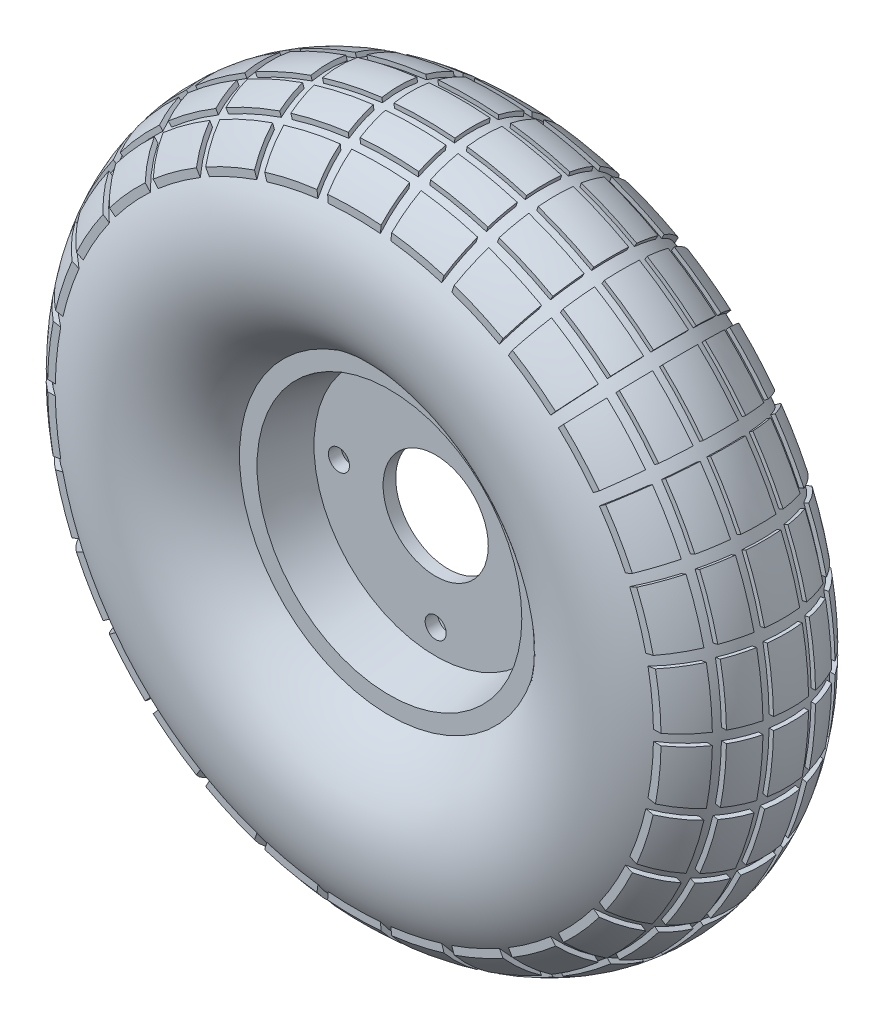
SolidWorks part; units mm, degrees
ref_plane "Front Plane" through (0, 0, 0) normal (0, 0, 1) x (1, 0, 0)
ref_plane "Top Plane" through (0, 0, 0) normal (0, 1, 0) x (1, 0, 0)
ref_plane "Right Plane" through (0, 0, 0) normal (1, 0, 0) x (0, 0, -1)
sketch "Sketch1" plane through (0, 0, 0) normal (1, 0, 0) x (0, 0, -1)
  line L0 (-19.05, 47.9669) -> (-19.05, 54.3169)
  line L1 (-19.05, 47.9669) -> (-2.286, 44.0981)
  line L2 (-2.286, 44.0981) -> (-2.286, 0)
  line L3 (-2.286, 0) -> (0, 0)
  line L4 (0, 0) -> (0, 52.3875)
  line L5 (0, 122.2375) -> (0, 125.4125)
  arc A0 (0, 125.4125) -> (-19.05, 54.3169) centre (0, 87.3125) ccw
  arc A1 (0, 122.2375) -> (0, 52.3875) centre (0, 87.3125) ccw
  dimension "D1" = 3.175
  dimension "D6" = 76.2
  dimension "D2" = 102.995
  dimension "D3" = 6.35
  dimension "D4" = 2.286
  dimension "D5" = 125.4125
  dimension "D7" = 19.05
  dimension "D8" = 52.3875
revolve "Revolve1" add sketch "Sketch1" angle 360 about L3
sketch "Sketch3" plane through (0, 0, 0) normal (1, 0, 0) x (0, 0, -1)
  line L0 (0, 125.4125) -> (0, 127)
  line L1 (-9.525, 125.84) -> (-9.525, 124.2027)
  line L3 (-19.05, 122.1291) -> (-19.05, 120.3081)
  line L5 (-22.225, 120.1933) -> (-22.225, 118.2586)
  line L7 (-31.75, 111.125) -> (-31.75, 108.3731)
  line L8 (-6.35, 126.4887) -> (-6.35, 124.8796)
  arc A0 (-19.05, -49.5544) -> (0, -120.65) centre (0, -82.55) ccw
  arc A1 (0, 127) -> (-6.35, 126.4887) centre (0, 87.3125) ccw
  arc A2 (0, 125.4125) -> (-19.05, 54.3169) centre (0, 87.3125) ccw
  arc A3 (0, 125.4125) -> (-6.35, 124.8796) centre (0, 87.3125) ccw
  arc A4 (-22.225, 118.2586) -> (-31.75, 108.3731) centre (0, 87.3125) ccw
  arc A5 (-9.525, 124.2027) -> (-19.05, 120.3081) centre (0, 87.3125) ccw
  arc A6 (-9.525, 125.84) -> (-19.05, 122.1291) centre (0, 87.3125) ccw
  arc A7 (-22.225, 120.1933) -> (-31.75, 111.125) centre (0, 87.3125) ccw
  dimension "D1" = 6.35
  dimension "D2" = 3.175
  dimension "D3" = 3.175
  dimension "D4" = 9.525
  dimension "D5" = 9.525
  dimension "D6" = 127
revolve "Revolve2" add sketch "Sketch3" angle 10 mid plane about axis through (0, 0, 2.286) along (0, 0, -1)
pattern_circular "CirPattern1" count 30 over 360 about axis through (0, 0, 0) along (0, 0, 1) of "Revolve2"
sketch "Sketch4" plane through (0, 0, 2.286) normal (0, 0, 1) x (1, 0, 0)
  circle A0 centre (0, 35.052) radius 3.81
  dimension "D1" = 7.62
  dimension "D2" = 35.052
sketch "Sketch6" plane through (0, 0, 2.286) normal (0, 0, 1) x (1, 0, 0)
  circle A0 centre (0, 0) radius 19.05
  dimension "D1" = 38.1
mirror "Mirror1" about plane through (0, 0, 0) normal (0, 0, 1) of "CirPattern1", "Revolve2", "Revolve1"
extrude "Cut-Extrude2" cut sketch "Sketch6" against normal blind 10.16
extrude "Cut-Extrude3" cut sketch "Sketch4" against normal up to next
pattern_circular "CirPattern2" count 4 over 360 about axis through (0, 0, 0) along (0, 0, 1) of "Cut-Extrude3"
ref_plane "Plane1" through (0, 0, 38.1) normal (0, 0, 1) x (1, 0, 0)
ref_plane "Plane2" through (0, 0, -38.1) normal (0, 0, -1) x (-1, 0, 0)
